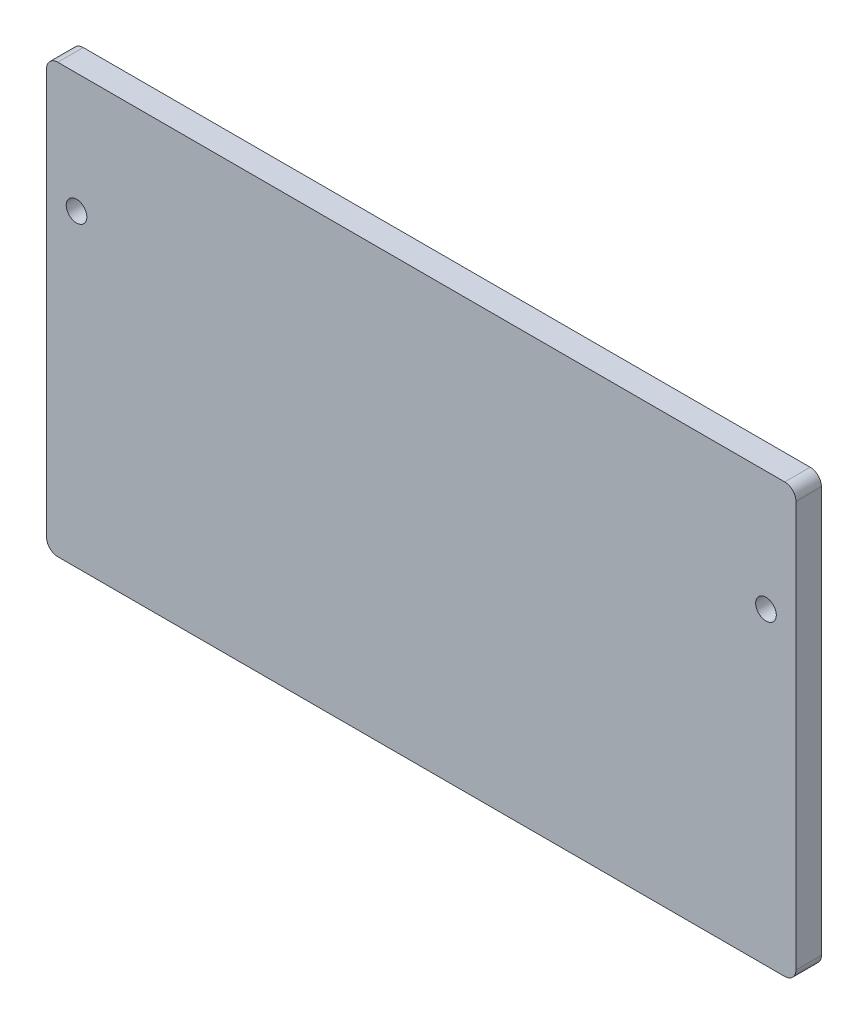
SolidWorks part; units mm, degrees
ref_plane "Front Plane" through (0, 0, 0) normal (0, 0, 1) x (1, 0, 0)
ref_plane "Top Plane" through (0, 0, 0) normal (0, 1, 0) x (1, 0, 0)
ref_plane "Right Plane" through (0, 0, 0) normal (1, 0, 0) x (0, 0, -1)
sketch "Sketch1" plane through (0, 0, 0) normal (0, 0, 1) x (1, 0, 0)
  line L1 (100, -57.15) -> (-100, -57.15)
  line L2 (100, -57.15) -> (100, 57.15)
  line L3 (100, 57.15) -> (-100, 57.15)
  line L4 (-100, -57.15) -> (-100, 57.15)
  line L5 (100, -57.15) -> (-100, 57.15) construction
  line L6 (100, 57.15) -> (-100, -57.15) construction
  point P0 (0, 0)
  dimension "D1" = 200
  dimension "D2" = 114.3
extrude "Boss-Extrude1" add sketch "Sketch1" along normal blind 6.8
sketch "Sketch2" plane through (0, 0, 6.8) normal (0, 0, 1) x (1, 0, 0)
  line L0 (100, 57.15) -> (-100, 57.15) construction
  circle A1 centre (-92, 25.25) radius 2.75
  dimension "D2" = 5.5
  dimension "D1" = 31.9
  dimension "D3" = 92
extrude "Cut-Extrude1" cut sketch "Sketch2" against normal blind 6.8
fillet "Fillet1" radius 3 2 edges at (-100, -57.15, 3.4) (-100, 57.15, 3.4)
mirror "Mirror2" about plane through (0, 0, 0) normal (1, 0, 0) of "Fillet1", "Cut-Extrude1"
